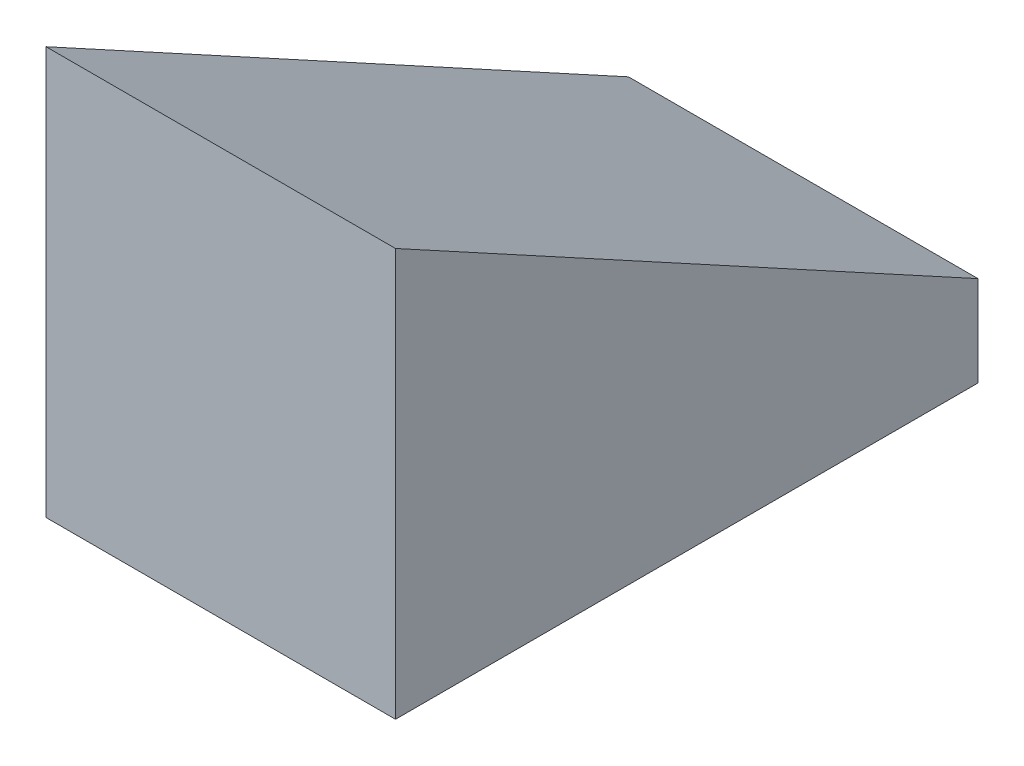
SolidWorks part; units mm, degrees
ref_plane "Спереди" through (0, 0, 0) normal (0, 0, 1) x (1, 0, 0)
ref_plane "Сверху" through (0, 0, 0) normal (0, 1, 0) x (1, 0, 0)
ref_plane "Справа" through (0, 0, 0) normal (1, 0, 0) x (0, 0, -1)
sketch "Sketch1" plane through (0, 0, 0) normal (1, 0, 0) x (0, 0, -1)
  line L0 (0, 0) -> (0, 70)
  line L1 (0, 70) -> (100, 15.5193)
  line L2 (100, 15.5193) -> (100, 0)
  line L3 (100, 0) -> (0, 0)
  dimension "D1" = 100
  dimension "D2" = 70
extrude "Boss-Extrude1" add sketch "Sketch1" along normal blind 60
